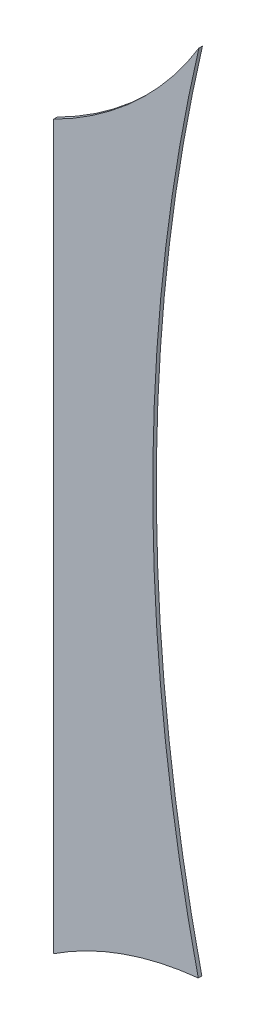
SolidWorks part; units mm, degrees
ref_plane "Alzado" through (0, 0, 0) normal (0, 0, 1) x (1, 0, 0)
ref_plane "Planta" through (0, 0, 0) normal (0, 1, 0) x (1, 0, 0)
ref_plane "Vista lateral" through (0, 0, 0) normal (1, 0, 0) x (0, 0, -1)
sketch "Model" plane through (0, 0, 0) normal (0, 0, 1) x (1, 0, 0)
  line L0 (53.1288, 12.5413) -> (53.1288, -7.6618)
  arc A0 (57.1746, -6.2271) -> (53.1288, -7.6618) centre (58.0734, -15.1835) ccw
  arc A1 (53.1288, 12.5413) -> (57.193, 16.2953) centre (48.6337, 21.4847) ccw
  arc A2 (57.193, 16.2953) -> (57.1746, -6.2271) centre (106.0606, 4.9943) ccw
extrude "Saliente-Extruir1" add sketch "Model" along normal blind 0.1
